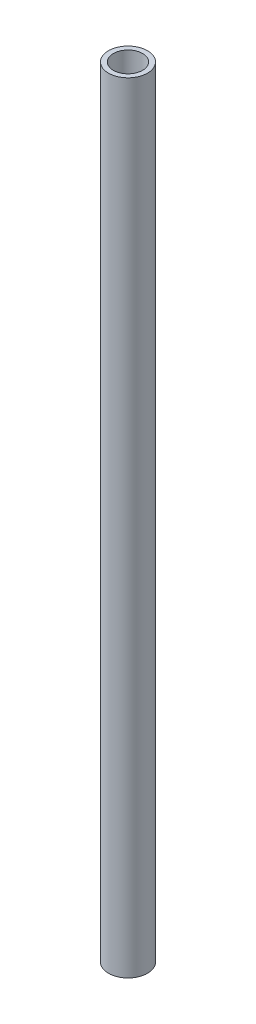
SolidWorks part; units mm, degrees
material "Copper"
ref_plane "Front Plane" through (0, 0, 0) normal (0, 0, 1) x (1, 0, 0)
ref_plane "Top Plane" through (0, 0, 0) normal (0, 1, 0) x (1, 0, 0)
ref_plane "Right Plane" through (0, 0, 0) normal (1, 0, 0) x (0, 0, -1)
sketch "Sketch1" plane through (0, 0, 0) normal (0, 1, 0) x (1, 0, 0)
  circle A0 centre (0, 0) radius 2
  circle A1 centre (0, 0) radius 1.5
  dimension "D1" = 4
  dimension "D2" = 3
extrude "Boss-Extrude1" add sketch "Sketch1" along normal mid plane 80
